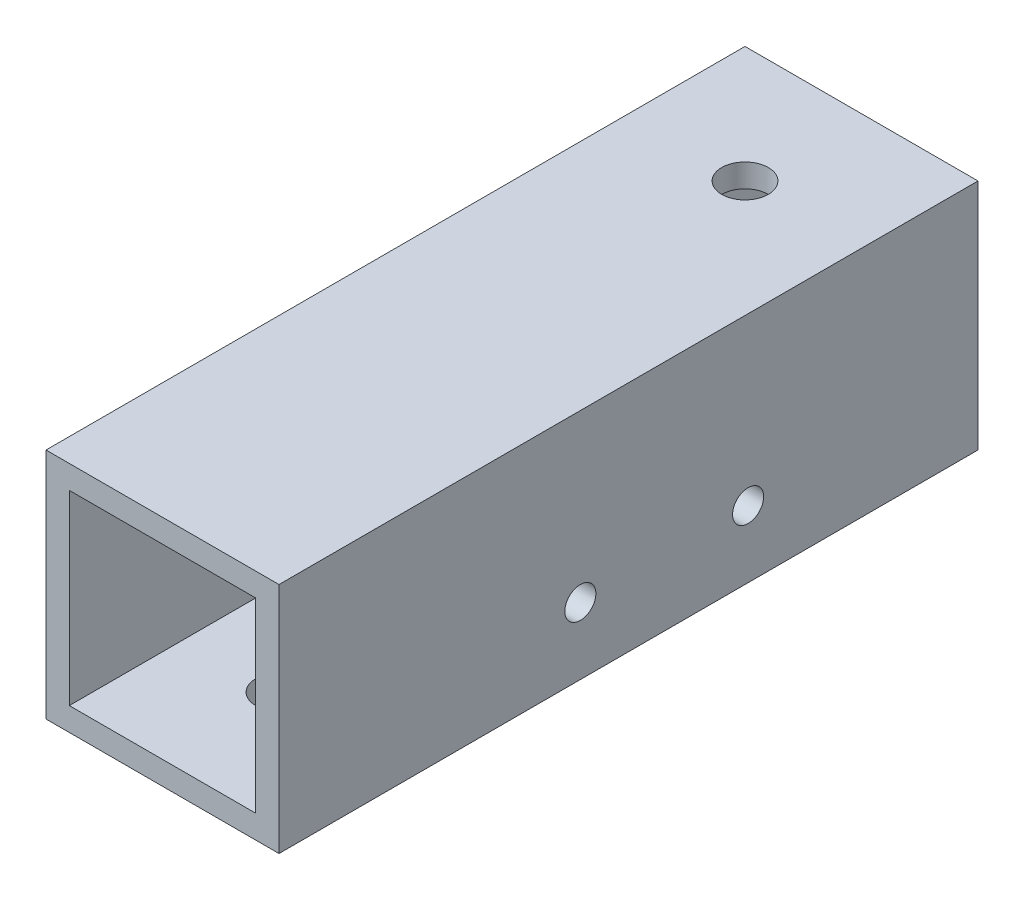
SolidWorks part; units mm, degrees
material "1060 合金"
ref_plane "正面" through (0, 0, 0) normal (0, 0, 1) x (1, 0, 0)
ref_plane "平面" through (0, 0, 0) normal (0, 1, 0) x (1, 0, 0)
ref_plane "右側面" through (0, 0, 0) normal (1, 0, 0) x (0, 0, -1)
sketch "ｽｹｯﾁ1" plane through (0, 0, 0) normal (0, 0, 1) x (1, 0, 0)
  line L1 (-7.0101, 7.7326) -> (7.9899, 7.7326)
  line L2 (-7.0101, 7.7326) -> (-7.0101, -7.2674)
  line L3 (-7.0101, -7.2674) -> (7.9899, -7.2674)
  line L4 (7.9899, 7.7326) -> (7.9899, -7.2674)
  line L9 (-5.5101, 6.2326) -> (6.4899, 6.2326)
  line L10 (-5.5101, 6.2326) -> (-5.5101, -5.7674)
  line L11 (-5.5101, -5.7674) -> (6.4899, -5.7674)
  line L12 (6.4899, 6.2326) -> (6.4899, -5.7674)
  dimension "D1" = 15
  dimension "D2" = 15
  dimension "D3" = 1.5
  dimension "D4" = 1.5
  dimension "D5" = 12
  dimension "D6" = 12
extrude "ﾎﾞｽ - 押し出し2" add sketch "ｽｹｯﾁ1" along normal blind 45
sketch "ｽｹｯﾁ2" plane through (0, 7.7326, 0) normal (0, 1, 0) x (1, 0, 0)
  line L0 (7.9899, 0) -> (-7.0101, 0) construction
  line L1 (7.9899, -45) -> (7.9899, 0) construction
  circle A0 centre (0.4899, -7.5) radius 1.5
  dimension "D1" = 7.5
  dimension "D2" = 7.5
extrude "ｶｯﾄ - 押し出し1" cut sketch "ｽｹｯﾁ2" against normal blind 10
sketch "ｽｹｯﾁ3" plane through (0, -7.2674, 0) normal (0, -1, 0) x (1, 0, 0)
  line L0 (-7.0101, 45) -> (7.9899, 45) construction
  line L1 (7.9899, 45) -> (7.9899, 0) construction
  circle A0 centre (0.4899, 37.5) radius 1.5
  dimension "D1" = 7.5
  dimension "D2" = 7.5
extrude "ｶｯﾄ - 押し出し2" cut sketch "ｽｹｯﾁ3" against normal blind 10
sketch "ｽｹｯﾁ4" plane through (7.9899, 0, 0) normal (1, 0, 0) x (0, 0, -1)
  line L0 (-45, -7.2674) -> (-45, 7.7326) construction
  line L1 (-45, -7.2674) -> (0, -7.2674) construction
  circle A0 centre (-25.6, -2.9674) radius 1
  dimension "D1" = 19.4
  dimension "D2" = 4.3
extrude "ｶｯﾄ - 押し出し3" cut sketch "ｽｹｯﾁ4" against normal blind 10
sketch "ｽｹｯﾁ5" plane through (7.9899, 0, 0) normal (1, 0, 0) x (0, 0, -1)
  circle A0 centre (-14.8, -2.9674) radius 1
  circle A1 centre (-25.6, -2.9674) radius 1 construction
  dimension "D1" = 10.8
extrude "ｶｯﾄ - 押し出し4" cut sketch "ｽｹｯﾁ5" against normal blind 10
